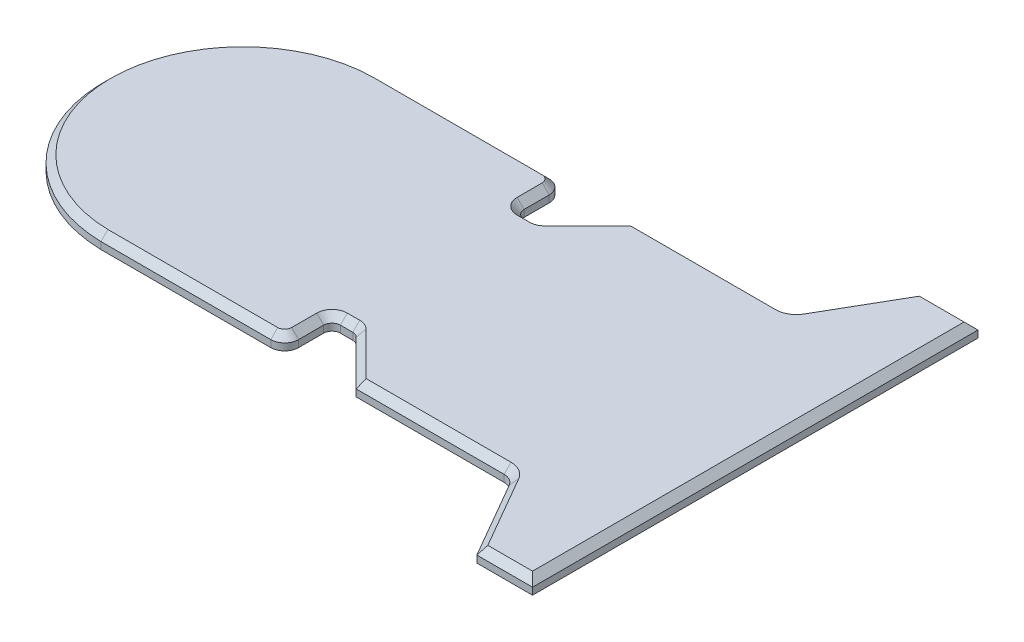
SolidWorks part; units mm, degrees
ref_plane "Front Plane" through (0, 0, 0) normal (0, 0, 1) x (1, 0, 0)
ref_plane "Top Plane" through (0, 0, 0) normal (0, 1, 0) x (1, 0, 0)
ref_plane "Right Plane" through (0, 0, 0) normal (1, 0, 0) x (0, 0, -1)
sketch "Sketch1" plane through (0, 0, 0) normal (0, 1, 0) x (1, 0, 0)
  line L0 (15.2546, 44.9902) -> (15.2546, 35.9902)
  line L1 (-50.7454, -49.9902) -> (10.2546, -49.9902)
  line L3 (-50.7454, 49.9902) -> (10.2546, 49.9902)
  line L5 (-50.7454, -49.9902) -> (50.7454, 49.9902) construction
  line L6 (-50.7454, 49.9902) -> (50.7454, -49.9902) construction
  line L7 (18.2546, 32.9902) -> (22.7119, 32.9902)
  line L8 (24.8333, 33.8689) -> (40.9546, 49.9902)
  line L9 (40.9546, 49.9902) -> (94.0678, 49.9902)
  line L10 (98.398, 52.4902) -> (114.2807, 80)
  line L11 (114.2807, 80) -> (134.2807, 80)
  line L12 (-49.7577, 0) -> (134.2807, 0) construction
  line L13 (134.2807, 80) -> (134.2807, -80)
  line L14 (40.9546, 49.9902) -> (96.9546, 49.9902)
  line L15 (40.9546, 49.9902) -> (50.7454, 49.9902)
  line L17 (114.2807, -80) -> (134.2807, -80)
  line L18 (98.398, -52.4902) -> (114.2807, -80)
  line L19 (40.9546, -49.9902) -> (94.0678, -49.9902)
  line L20 (18.2546, -32.9902) -> (22.7119, -32.9902)
  line L21 (24.8333, -33.8689) -> (40.9546, -49.9902)
  line L22 (15.2546, -44.9902) -> (15.2546, -35.9902)
  line L23 (40.9546, -49.9902) -> (50.7454, -49.9902)
  arc A0 (-50.7454, 49.9902) -> (-50.7454, -49.9902) centre (-49.7577, 0) ccw
  arc A1 (22.7119, 32.9902) -> (24.8333, 33.8689) centre (22.7119, 35.9902) ccw
  arc A2 (18.2546, 32.9902) -> (15.2546, 35.9902) centre (18.2546, 35.9902) cw
  arc A3 (15.2546, 44.9902) -> (10.2546, 49.9902) centre (10.2546, 44.9902) ccw
  arc A4 (15.2546, -44.9902) -> (10.2546, -49.9902) centre (10.2546, -44.9902) cw
  arc A5 (22.7119, -32.9902) -> (24.8333, -33.8689) centre (22.7119, -35.9902) cw
  arc A6 (18.2546, -32.9902) -> (15.2546, -35.9902) centre (18.2546, -35.9902) ccw
  arc A7 (98.398, -52.4902) -> (94.0678, -49.9902) centre (94.0678, -54.9902) ccw
  arc A8 (98.398, 52.4902) -> (94.0678, 49.9902) centre (94.0678, 54.9902) cw
  point P0 (0, 0)
  point P24 (23.9546, 32.9902)
  point P27 (15.2546, 32.9902)
  point P30 (15.2546, 49.9902)
  point P33 (15.2546, -49.9902)
  point P37 (23.9546, -32.9902)
  point P40 (15.2546, -32.9902)
  point P43 (96.9546, -49.9902)
  dimension "D2" = 100
  dimension "D11" = 3
  dimension "D12" = 5
  dimension "D13" = 5
  dimension "D14" = 3
  dimension "D15" = 5
  dimension "D1" = 120
  dimension "D3" = 8.7
  dimension "D4" = 135
  dimension "D5" = 17
  dimension "D6" = 56
  dimension "D7" = 160
  dimension "D8" = 20
  dimension "D10" = 66
extrude "Boss-Extrude1" add sketch "Sketch1" along normal blind 5
sketch "Sketch4" plane through (0, 5, 0) normal (0, 1, 0) x (1, 0, 0)
  line L0 (22.7119, 32.9902) -> (22.7119, -32.9902) construction
  line L1 (22.7119, 0) -> (-0.2253, 0) construction
  line L2 (22.7119, 21) -> (13.7119, 21)
  line L3 (10.7119, 18) -> (10.7119, -18)
  line L4 (13.7119, -21) -> (22.7119, -21)
  line L5 (10.7119, 21) -> (22.7119, -21) construction
  line L6 (22.7119, 21) -> (10.7119, -21) construction
  line L7 (22.7119, 21) -> (22.7119, -21)
  arc A0 (13.7119, -21) -> (10.7119, -18) centre (13.7119, -18) cw
  arc A1 (10.7119, 18) -> (13.7119, 21) centre (13.7119, 18) cw
  point P8 (16.7119, 0)
  dimension "D3" = 3
  dimension "D1" = 42
  dimension "D2" = 12
extrude "Cut-Extrude2" [suppressed] cut sketch "Sketch4" against normal through all
chamfer "Chamfer1" distance 2.5 angle 45 24 edges at (124.2807, 5, -80) (134.2807, 5, 0) (124.2807, 5, 80) (106.3393, 5, 66.2451) (96.5678, 5, 50.6601) (67.5112, 5, 49.9902) (32.8939, 5, 41.9296) (23.86, 5, 33.2186) (20.4833, 5, 32.9902) (16.1333, 5, 33.8689) (15.2546, 5, 40.4902) (13.7901, 5, 48.5258) (-20.2454, 5, 49.9902) (-99.7577, 5, 0) (-20.2454, 5, -49.9902) (13.7901, 5, -48.5258) (15.2546, 5, -40.4902) (16.1333, 5, -33.8689) (20.4833, 5, -32.9902) (23.86, 5, -33.2186) (32.8939, 5, -41.9296) (67.5112, 5, -49.9902) (96.5678, 5, -50.6601) (106.3393, 5, -66.2451)
